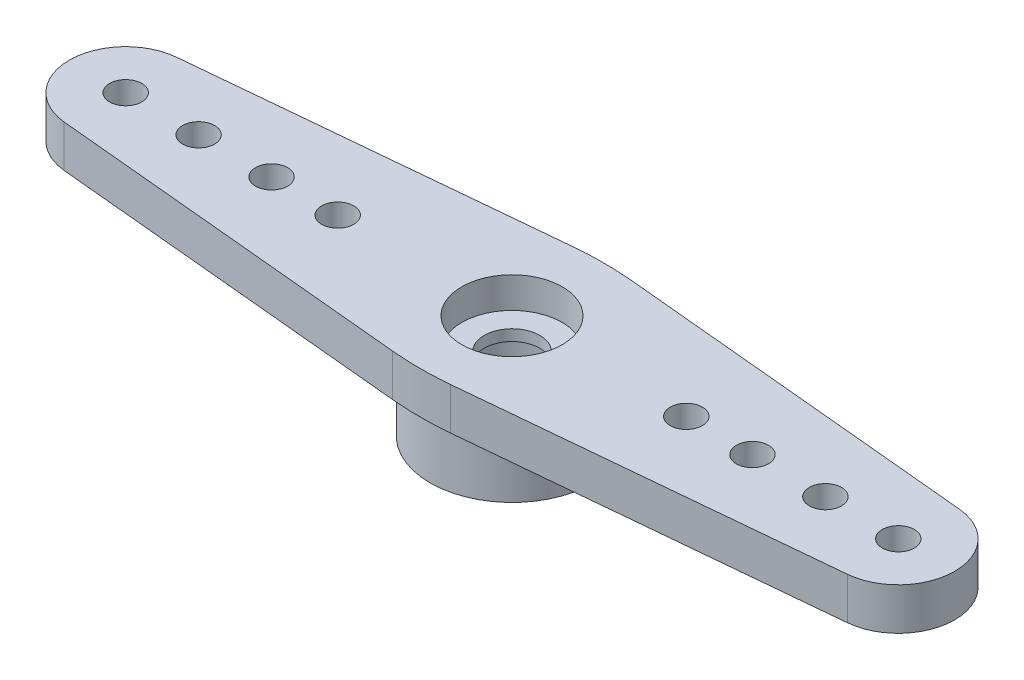
SolidWorks part; units mm, degrees
ref_plane "Front Plane" through (0, 0, 0) normal (0, 0, 1) x (1, 0, 0)
ref_plane "Top Plane" through (0, 0, 0) normal (0, 1, 0) x (1, 0, 0)
ref_plane "Right Plane" through (0, 0, 0) normal (1, 0, 0) x (0, 0, -1)
sketch "Sketch1" plane through (0, 0, 0) normal (0, 1, 0) x (1, 0, 0)
  circle A0 centre (0, 0) radius 3.3655
  circle A1 centre (0, 0) radius 2.2352
  dimension "D1" = 6.731
  dimension "D2" = 4.4704
extrude "Boss-Extrude1" add sketch "Sketch1" along normal blind 2.54
sketch "Sketch2" plane through (0, 2.54, 0) normal (0, 1, 0) x (1, 0, 0)
  line L0 (0, 0) -> (50000, 0) construction
  line L1 (0, 0) -> (0, 50000) construction
  line L2 (0, 3.8227) -> (16.0923, 2.3075)
  line L3 (0, -3.8227) -> (16.0923, -2.3075)
  line L4 (0, -3.8227) -> (-16.0923, -2.3075)
  line L5 (0, 3.8227) -> (-16.0923, 2.3075)
  circle A0 centre (15.875, 0) radius 0.6604
  circle A1 centre (12.8778, 0) radius 0.6604
  circle A2 centre (9.8806, 0) radius 0.6604
  circle A3 centre (7.1628, 0) radius 0.6604
  circle A4 centre (15.875, 0) radius 2.3178
  circle A5 centre (0, 0) radius 3.8227
  circle A6 centre (-15.875, 0) radius 2.3178
  circle A7 centre (-7.1628, 0) radius 0.6604
  circle A8 centre (-9.8806, 0) radius 0.6604
  circle A9 centre (-12.8778, 0) radius 0.6604
  circle A10 centre (-15.875, 0) radius 0.6604
  circle A11 centre (0, 0) radius 1.143
  circle M1 centre (0, 0) radius 3.3655
  circle M2 centre (0, 0) radius 2.2352
  dimension "D1" = 1.3208
  dimension "D6" = 4.6355
  dimension "D7" = 7.6454
  dimension "D8" = 2.286
  dimension "D2" = 15.875
  dimension "D3" = 2.9972
  dimension "D4" = 5.9944
  dimension "D5" = 8.7122
extrude "Boss-Extrude2" add sketch "Sketch2" along normal blind 1.7272 contours L5 A6 L4 A5 A8 A7 A9 | A6 A10 | A5 L3 A4 L2 A1 A2 A3 | A4 A0 | M1 M2 | L3 A5 L2 L5 L4 M1 | A11 M2
fillet "Fillet1" radius 12.7 2 edges at (0, 3.4036, -3.8227) (0, 3.4036, 3.8227)
sketch "Sketch3" plane through (0, 4.2672, 0) normal (0, 1, 0) x (1, 0, 0)
  circle A0 centre (0, 0) radius 2.0638
  circle M17 centre (0, 0) radius 1.143
  dimension "D1" = 4.1275
extrude "Cut-Extrude1" cut sketch "Sketch3" against normal blind 1.27 contours A0 M17
